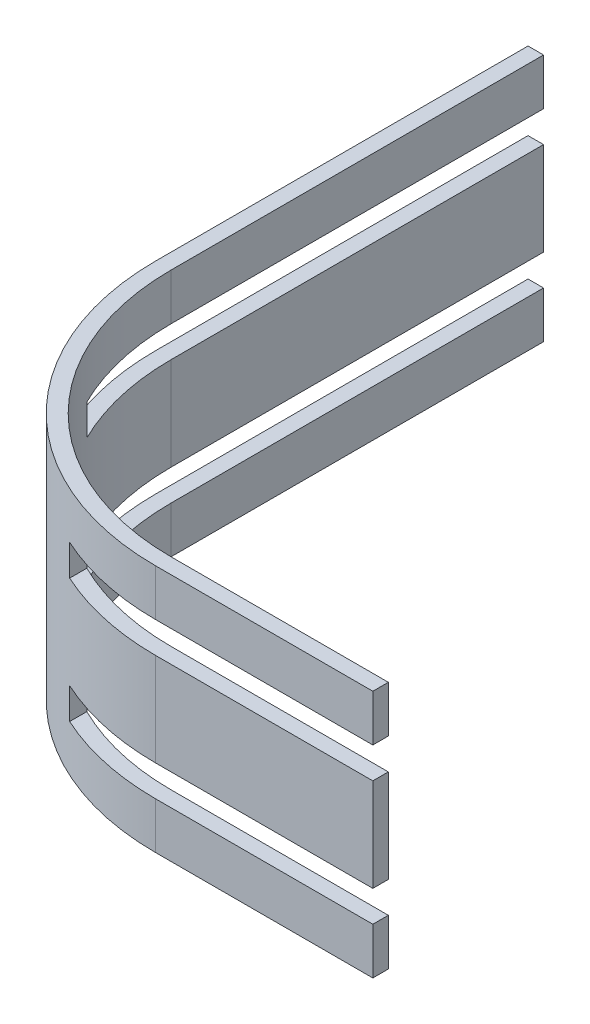
SolidWorks part; units mm, degrees
ref_plane "Front Plane" through (0, 0, 0) normal (0, 0, 1) x (1, 0, 0)
ref_plane "Top Plane" through (0, 0, 0) normal (0, 1, 0) x (1, 0, 0)
ref_plane "Right Plane" through (0, 0, 0) normal (1, 0, 0) x (0, 0, -1)
sketch "Sketch1" plane through (0, 0, 0) normal (0, 1, 0) x (1, 0, 0)
  line L0 (-15, 20) -> (-15, -4)
  line L1 (1, -20) -> (15, -20)
  line L2 (15, -20) -> (15, -21)
  line L3 (15, -21) -> (1, -21)
  line L4 (-16, -4) -> (-16, 20)
  line L5 (-16, 20) -> (-15, 20)
  arc A0 (-15, -4) -> (1, -20) centre (1, -4) ccw
  arc A1 (-16, -4) -> (1, -21) centre (1, -4) ccw
  dimension "D7" = 16
  dimension "D8" = 17
  dimension "D1" = 30
  dimension "D2" = 40
  dimension "D3" = 20
  dimension "D4" = 15
  dimension "D5" = 1
  dimension "D6" = 1
extrude "Extrude1" add sketch "Sketch1" along normal blind 6
sketch "Sketch2" plane through (0, 6, 0) normal (0, 1, 0) x (1, 0, 0)
  line L0 (-6.075, -18.3508) -> (-6.075, -19.4578)
  line L1 (-14.4578, -11.075) -> (-13.3508, -11.075)
  line L2 (-15, -4) -> (-15, 20) construction
  line L3 (15, -20) -> (1, -20) construction
  arc A0 (-16, -4) -> (1, -21) centre (1, -4) ccw construction
  arc A1 (-15, -4) -> (1, -20) centre (1, -4) ccw construction
  arc A2 (-14.4578, -11.075) -> (-6.075, -19.4578) centre (1, -4) ccw
  arc A3 (-13.3508, -11.075) -> (-6.075, -18.3508) centre (1, -4) ccw
  dimension "D1" = 8.925
  dimension "D2" = 8.925
extrude "Extrude2" add sketch "Sketch2" along normal blind 2
sketch "Sketch3" plane through (0, 0, 0) normal (0, -1, 0) x (1, 0, 0)
  line L0 (-14.4578, 11.075) -> (-13.3508, 11.075)
  line L1 (-6.075, 19.4578) -> (-6.075, 18.3508)
  line L2 (-15, 4) -> (-15, -20) construction
  line L3 (15, 20) -> (1, 20) construction
  arc A0 (1, 21) -> (-16, 4) centre (1, 4) ccw construction
  arc A1 (1, 20) -> (-15, 4) centre (1, 4) ccw construction
  arc A2 (-6.075, 19.4578) -> (-14.4578, 11.075) centre (1, 4) ccw
  arc A3 (-6.075, 18.3508) -> (-13.3508, 11.075) centre (1, 4) ccw
  dimension "D1" = 8.925
  dimension "D2" = 8.925
extrude "Extrude3" add sketch "Sketch3" along normal blind 2
sketch "Sketch4" plane through (0, 8, 0) normal (0, 1, 0) x (1, 0, 0)
  line L0 (15, -21) -> (15, -20) construction
  line L1 (15, -20) -> (1, -20) construction
  line L2 (1, -21) -> (15, -21) construction
  line L3 (-16, 20) -> (-16, -4) construction
  line L4 (-15, -4) -> (-15, 20) construction
  line L5 (-15, 20) -> (-16, 20) construction
  line L6 (15, -21) -> (15, -20)
  line L7 (15, -20) -> (1, -20)
  line L8 (1, -21) -> (15, -21)
  line L9 (-16, 20) -> (-16, -4)
  line L10 (-15, -4) -> (-15, 20)
  line L11 (-15, 20) -> (-16, 20)
  arc A0 (-6.075, -19.4578) -> (1, -21) centre (1, -4) ccw construction
  arc A1 (-6.075, -18.3508) -> (1, -20) centre (1, -4) ccw construction
  arc A2 (-14.4578, -11.075) -> (-6.075, -19.4578) centre (1, -4) ccw construction
  arc A3 (-13.3508, -11.075) -> (-6.075, -18.3508) centre (1, -4) ccw construction
  arc A4 (-15, -4) -> (-13.3508, -11.075) centre (1, -4) ccw construction
  arc A5 (-16, -4) -> (-14.4578, -11.075) centre (1, -4) ccw construction
  arc A6 (-6.075, -19.4578) -> (1, -21) centre (1, -4) ccw
  arc A7 (-6.075, -18.3508) -> (1, -20) centre (1, -4) ccw
  arc A8 (-14.4578, -11.075) -> (-6.075, -19.4578) centre (1, -4) ccw
  arc A9 (-13.3508, -11.075) -> (-6.075, -18.3508) centre (1, -4) ccw
  arc A10 (-15, -4) -> (-13.3508, -11.075) centre (1, -4) ccw
  arc A11 (-16, -4) -> (-14.4578, -11.075) centre (1, -4) ccw
extrude "Extrude4" add sketch "Sketch4" along normal blind 3
sketch "Sketch5" plane through (0, -2, 0) normal (0, -1, 0) x (1, 0, 0)
  line L0 (-16, -20) -> (-16, 4) construction
  line L1 (-15, 4) -> (-15, -20) construction
  line L2 (1, 21) -> (15, 21) construction
  line L3 (15, 20) -> (1, 20) construction
  line L4 (15, 21) -> (15, 20) construction
  line L5 (-15, -20) -> (-16, -20) construction
  line L6 (-16, -20) -> (-16, 4)
  line L7 (-15, 4) -> (-15, -20)
  line L8 (1, 21) -> (15, 21)
  line L9 (15, 20) -> (1, 20)
  line L10 (15, 21) -> (15, 20)
  line L11 (-15, -20) -> (-16, -20)
  arc A0 (-13.3508, 11.075) -> (-15, 4) centre (1, 4) ccw construction
  arc A1 (-14.4578, 11.075) -> (-16, 4) centre (1, 4) ccw construction
  arc A2 (-6.075, 19.4578) -> (-14.4578, 11.075) centre (1, 4) ccw construction
  arc A3 (-6.075, 18.3508) -> (-13.3508, 11.075) centre (1, 4) ccw construction
  arc A4 (1, 20) -> (-6.075, 18.3508) centre (1, 4) ccw construction
  arc A5 (1, 21) -> (-6.075, 19.4578) centre (1, 4) ccw construction
  arc A6 (-13.3508, 11.075) -> (-15, 4) centre (1, 4) ccw
  arc A7 (-14.4578, 11.075) -> (-16, 4) centre (1, 4) ccw
  arc A8 (-6.075, 19.4578) -> (-14.4578, 11.075) centre (1, 4) ccw
  arc A9 (-6.075, 18.3508) -> (-13.3508, 11.075) centre (1, 4) ccw
  arc A10 (1, 20) -> (-6.075, 18.3508) centre (1, 4) ccw
  arc A11 (1, 21) -> (-6.075, 19.4578) centre (1, 4) ccw
extrude "Extrude5" add sketch "Sketch5" along normal blind 3
